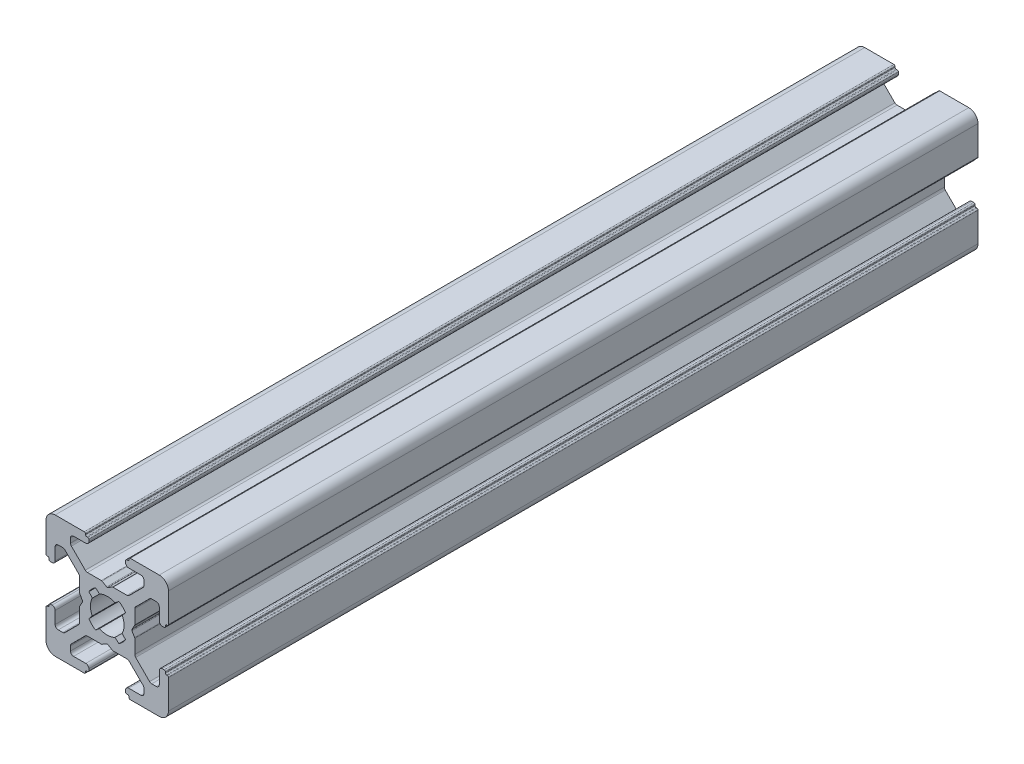
SolidWorks part; units mm, degrees
ref_plane "Front Plane" through (0, 0, 0) normal (0, 0, 1) x (1, 0, 0)
ref_plane "Top Plane" through (0, 0, 0) normal (0, 1, 0) x (1, 0, 0)
ref_plane "Right Plane" through (0, 0, 0) normal (1, 0, 0) x (0, 0, -1)
sketch "Sketch1" plane through (0, 0, 0) normal (0, 0, 1) x (1, 0, 0)
  line L0 (0, 13.3675) -> (0, -10.9159) construction
  line L1 (-12.9725, 0) -> (15.1887, 0) construction
  line L2 (-3.5, 8.5) -> (-5.5, 8.5)
  line L3 (-3.55, 9.7) -> (-3.55, 9.8)
  line L4 (-6, 7.2678) -> (-6, 8)
  line L5 (-7.2678, 6) -> (-8, 6)
  line L6 (-3.75, 10) -> (-8.5, 10)
  line L7 (-9.7, 3.55) -> (-9.8, 3.55)
  line L8 (-9.5, 3.2) -> (-9.5, 3.35)
  line L9 (-9, 3) -> (-9.3, 3)
  line L10 (-4.4732, 0.8536) -> (-4.0381, 0.1)
  line L11 (-4.5, 3.2322) -> (-4.5, 0.9536)
  line L12 (-8.5, 3.5) -> (-8.5, 5.5)
  line L13 (-10, 3.75) -> (-10, 8.5)
  line L14 (-3.5858, 4.6464) -> (-5.8536, 6.9142)
  line L15 (-4.6464, 3.5858) -> (-6.9142, 5.8536)
  line L16 (-3.2, 9.5) -> (-3.35, 9.5)
  line L17 (-3, 9) -> (-3, 9.3)
  line L18 (-0.8536, 4.4732) -> (-0.1, 4.0381)
  line L19 (-3.2322, 4.5) -> (-0.9536, 4.5)
  line L20 (-1.2582, 2.4453) -> (-1.9139, 2.9896)
  line L21 (-2.4453, 1.2582) -> (-2.9922, 1.9099)
  line L22 (3.5, -8.5) -> (5.5, -8.5)
  line L23 (3.55, -9.7) -> (3.55, -9.8)
  line L24 (6, -7.2678) -> (6, -8)
  line L25 (7.2678, -6) -> (8, -6)
  line L26 (3.75, -10) -> (8.5, -10)
  line L27 (9.7, -3.55) -> (9.8, -3.55)
  line L28 (9.5, -3.2) -> (9.5, -3.35)
  line L29 (9, -3) -> (9.3, -3)
  line L30 (4.4732, -0.8536) -> (4.0381, -0.1)
  line L31 (4.5, -3.2322) -> (4.5, -0.9536)
  line L32 (8.5, -3.5) -> (8.5, -5.5)
  line L33 (10, -3.75) -> (10, -8.5)
  line L34 (3.5858, -4.6464) -> (5.8536, -6.9142)
  line L35 (4.6464, -3.5858) -> (6.9142, -5.8536)
  line L36 (3.2, -9.5) -> (3.35, -9.5)
  line L37 (3, -9) -> (3, -9.3)
  line L38 (0.8536, -4.4732) -> (0.1, -4.0381)
  line L39 (3.2322, -4.5) -> (0.9536, -4.5)
  line L40 (1.2582, -2.4453) -> (1.9139, -2.9896)
  line L41 (2.4453, -1.2582) -> (2.9922, -1.9099)
  line L42 (-2.4453, -1.2582) -> (-2.9922, -1.9099)
  line L43 (-1.2582, -2.4453) -> (-1.9139, -2.9896)
  line L44 (-3.2322, -4.5) -> (-0.9536, -4.5)
  line L45 (-0.8536, -4.4732) -> (-0.1, -4.0381)
  line L46 (-3, -9) -> (-3, -9.3)
  line L47 (-3.2, -9.5) -> (-3.35, -9.5)
  line L48 (-4.6464, -3.5858) -> (-6.9142, -5.8536)
  line L49 (-3.5858, -4.6464) -> (-5.8536, -6.9142)
  line L50 (-10, -3.75) -> (-10, -8.5)
  line L51 (-8.5, -3.5) -> (-8.5, -5.5)
  line L52 (-4.5, -3.2322) -> (-4.5, -0.9536)
  line L53 (-4.4732, -0.8536) -> (-4.0381, -0.1)
  line L54 (-9, -3) -> (-9.3, -3)
  line L55 (-9.5, -3.2) -> (-9.5, -3.35)
  line L56 (-9.7, -3.55) -> (-9.8, -3.55)
  line L57 (2.4453, 1.2582) -> (2.9922, 1.9099)
  line L58 (1.2582, 2.4453) -> (1.9139, 2.9896)
  line L59 (3.2322, 4.5) -> (0.9536, 4.5)
  line L60 (0.8536, 4.4732) -> (0.1, 4.0381)
  line L61 (-3.75, -10) -> (-8.5, -10)
  line L62 (-7.2678, -6) -> (-8, -6)
  line L63 (-6, -7.2678) -> (-6, -8)
  line L64 (3, 9) -> (3, 9.3)
  line L65 (3.2, 9.5) -> (3.35, 9.5)
  line L66 (4.6464, 3.5858) -> (6.9142, 5.8536)
  line L67 (3.5858, 4.6464) -> (5.8536, 6.9142)
  line L68 (10, 3.75) -> (10, 8.5)
  line L69 (8.5, 3.5) -> (8.5, 5.5)
  line L70 (4.5, 3.2322) -> (4.5, 0.9536)
  line L71 (4.4732, 0.8536) -> (4.0381, 0.1)
  line L72 (9, 3) -> (9.3, 3)
  line L73 (9.5, 3.2) -> (9.5, 3.35)
  line L74 (9.7, 3.55) -> (9.8, 3.55)
  line L75 (3.75, 10) -> (8.5, 10)
  line L76 (7.2678, 6) -> (8, 6)
  line L77 (6, 7.2678) -> (6, 8)
  line L78 (3.55, 9.7) -> (3.55, 9.8)
  line L79 (3.5, 8.5) -> (5.5, 8.5)
  line L80 (-3.55, -9.7) -> (-3.55, -9.8)
  line L81 (-3.5, -8.5) -> (-5.5, -8.5)
  arc A0 (-10, 8.5) -> (-8.5, 10) centre (-8.5, 8.5) cw
  arc A1 (-8.5, 5.5) -> (-8, 6) centre (-8, 5.5) cw
  arc A2 (-7.2678, 6) -> (-6.9142, 5.8536) centre (-7.2678, 5.5) cw
  arc A3 (-5.8536, 6.9142) -> (-6, 7.2678) centre (-5.5, 7.2678) cw
  arc A4 (-6, 8) -> (-5.5, 8.5) centre (-5.5, 8) cw
  arc A5 (-9.7, 3.55) -> (-9.5, 3.35) centre (-9.7, 3.35) cw
  arc A6 (-9.8, 3.55) -> (-10, 3.75) centre (-9.8, 3.75) cw
  arc A7 (-9.3, 3) -> (-9.5, 3.2) centre (-9.3, 3.2) cw
  arc A8 (-8.5, 3.5) -> (-9, 3) centre (-9, 3.5) cw
  arc A9 (-4.6464, 3.5858) -> (-4.5, 3.2322) centre (-5, 3.2322) cw
  arc A10 (-4.4732, 0.8536) -> (-4.5, 0.9536) centre (-4.3, 0.9536) cw
  arc A11 (-4.0381, 0.1) -> (-4.0381, -0.1) centre (-4.2113, 0) cw
  arc A12 (-3.2, 9.5) -> (-3, 9.3) centre (-3.2, 9.3) cw
  arc A13 (-0.9536, 4.5) -> (-0.8536, 4.4732) centre (-0.9536, 4.3) cw
  arc A14 (-2.9922, 1.9099) -> (-1.9139, 2.9896) centre (0, 0) cw
  arc A15 (-3.2322, 4.5) -> (-3.5858, 4.6464) centre (-3.2322, 5) cw
  arc A16 (-3.75, 10) -> (-3.55, 9.8) centre (-3.75, 9.8) cw
  arc A17 (-3.35, 9.5) -> (-3.55, 9.7) centre (-3.35, 9.7) cw
  arc A18 (2.4453, -1.2582) -> (2.4453, 1.2582) centre (0, 0) ccw
  arc A19 (-3, 9) -> (-3.5, 8.5) centre (-3.5, 9) cw
  arc A20 (-2.4453, -1.2582) -> (-2.4453, 1.2582) centre (0, 0) cw
  arc A21 (10, -8.5) -> (8.5, -10) centre (8.5, -8.5) cw
  arc A22 (8.5, -5.5) -> (8, -6) centre (8, -5.5) cw
  arc A23 (7.2678, -6) -> (6.9142, -5.8536) centre (7.2678, -5.5) cw
  arc A24 (5.8536, -6.9142) -> (6, -7.2678) centre (5.5, -7.2678) cw
  arc A25 (6, -8) -> (5.5, -8.5) centre (5.5, -8) cw
  arc A26 (9.7, -3.55) -> (9.5, -3.35) centre (9.7, -3.35) cw
  arc A27 (9.8, -3.55) -> (10, -3.75) centre (9.8, -3.75) cw
  arc A28 (9.3, -3) -> (9.5, -3.2) centre (9.3, -3.2) cw
  arc A29 (8.5, -3.5) -> (9, -3) centre (9, -3.5) cw
  arc A30 (4.6464, -3.5858) -> (4.5, -3.2322) centre (5, -3.2322) cw
  arc A31 (4.4732, -0.8536) -> (4.5, -0.9536) centre (4.3, -0.9536) cw
  arc A32 (3.2, -9.5) -> (3, -9.3) centre (3.2, -9.3) cw
  arc A33 (-0.1, -4.0381) -> (0.1, -4.0381) centre (0, -4.2113) cw
  arc A34 (0.9536, -4.5) -> (0.8536, -4.4732) centre (0.9536, -4.3) cw
  arc A35 (2.9922, -1.9099) -> (1.9139, -2.9896) centre (0, 0) cw
  arc A36 (1.2582, -2.4453) -> (-1.2582, -2.4453) centre (0, 0) cw
  arc A37 (3.2322, -4.5) -> (3.5858, -4.6464) centre (3.2322, -5) cw
  arc A38 (3.75, -10) -> (3.55, -9.8) centre (3.75, -9.8) cw
  arc A39 (3.35, -9.5) -> (3.55, -9.7) centre (3.35, -9.7) cw
  arc A40 (3, -9) -> (3.5, -8.5) centre (3.5, -9) cw
  arc A41 (-3, -9) -> (-3.5, -8.5) centre (-3.5, -9) ccw
  arc A42 (-3.35, -9.5) -> (-3.55, -9.7) centre (-3.35, -9.7) ccw
  arc A43 (-3.75, -10) -> (-3.55, -9.8) centre (-3.75, -9.8) ccw
  arc A44 (-3.2322, -4.5) -> (-3.5858, -4.6464) centre (-3.2322, -5) ccw
  arc A45 (-2.9922, -1.9099) -> (-1.9139, -2.9896) centre (0, 0) ccw
  arc A46 (-0.9536, -4.5) -> (-0.8536, -4.4732) centre (-0.9536, -4.3) ccw
  arc A47 (-3.2, -9.5) -> (-3, -9.3) centre (-3.2, -9.3) ccw
  arc A48 (-4.4732, -0.8536) -> (-4.5, -0.9536) centre (-4.3, -0.9536) ccw
  arc A49 (3, 9) -> (3.5, 8.5) centre (3.5, 9) ccw
  arc A50 (3.35, 9.5) -> (3.55, 9.7) centre (3.35, 9.7) ccw
  arc A51 (3.75, 10) -> (3.55, 9.8) centre (3.75, 9.8) ccw
  arc A52 (3.2322, 4.5) -> (3.5858, 4.6464) centre (3.2322, 5) ccw
  arc A53 (1.2582, 2.4453) -> (-1.2582, 2.4453) centre (0, 0) ccw
  arc A54 (-4.6464, -3.5858) -> (-4.5, -3.2322) centre (-5, -3.2322) ccw
  arc A55 (-8.5, -3.5) -> (-9, -3) centre (-9, -3.5) ccw
  arc A56 (-9.3, -3) -> (-9.5, -3.2) centre (-9.3, -3.2) ccw
  arc A57 (-9.8, -3.55) -> (-10, -3.75) centre (-9.8, -3.75) ccw
  arc A58 (-9.7, -3.55) -> (-9.5, -3.35) centre (-9.7, -3.35) ccw
  arc A59 (-6, -8) -> (-5.5, -8.5) centre (-5.5, -8) ccw
  arc A60 (2.9922, 1.9099) -> (1.9139, 2.9896) centre (0, 0) ccw
  arc A61 (0.9536, 4.5) -> (0.8536, 4.4732) centre (0.9536, 4.3) ccw
  arc A62 (-0.1, 4.0381) -> (0.1, 4.0381) centre (0, 4.2113) ccw
  arc A63 (-5.8536, -6.9142) -> (-6, -7.2678) centre (-5.5, -7.2678) ccw
  arc A64 (-7.2678, -6) -> (-6.9142, -5.8536) centre (-7.2678, -5.5) ccw
  arc A65 (-8.5, -5.5) -> (-8, -6) centre (-8, -5.5) ccw
  arc A66 (-10, -8.5) -> (-8.5, -10) centre (-8.5, -8.5) ccw
  arc A67 (3.2, 9.5) -> (3, 9.3) centre (3.2, 9.3) ccw
  arc A68 (4.0381, 0.1) -> (4.0381, -0.1) centre (4.2113, 0) ccw
  arc A69 (4.4732, 0.8536) -> (4.5, 0.9536) centre (4.3, 0.9536) ccw
  arc A70 (4.6464, 3.5858) -> (4.5, 3.2322) centre (5, 3.2322) ccw
  arc A71 (8.5, 3.5) -> (9, 3) centre (9, 3.5) ccw
  arc A72 (9.3, 3) -> (9.5, 3.2) centre (9.3, 3.2) ccw
  arc A73 (9.8, 3.55) -> (10, 3.75) centre (9.8, 3.75) ccw
  arc A74 (9.7, 3.55) -> (9.5, 3.35) centre (9.7, 3.35) ccw
  arc A75 (6, 8) -> (5.5, 8.5) centre (5.5, 8) ccw
  arc A76 (5.8536, 6.9142) -> (6, 7.2678) centre (5.5, 7.2678) ccw
  arc A77 (7.2678, 6) -> (6.9142, 5.8536) centre (7.2678, 5.5) ccw
  arc A78 (8.5, 5.5) -> (8, 6) centre (8, 5.5) ccw
  arc A79 (10, 8.5) -> (8.5, 10) centre (8.5, 8.5) ccw
  dimension "D4" = 5.5
  dimension "D1" = 6
  dimension "D2" = 20
  dimension "D3" = 20
  dimension "D5" = 5.5
  dimension "D6" = 10
  dimension "D7" = 6
  dimension "D8" = 6
  dimension "D9" = 6
extrude "Extrude1" add sketch "Sketch1" along normal blind 132.23
